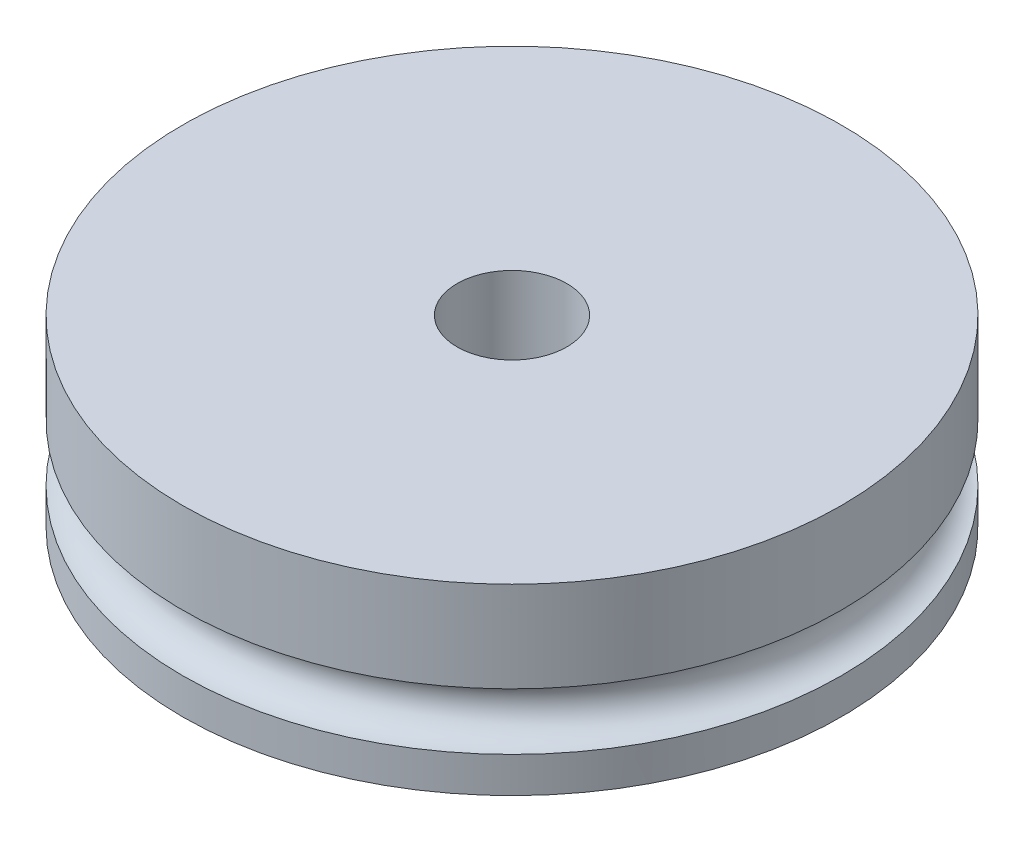
SolidWorks part; units mm, degrees
ref_plane "Front Plane" through (0, 0, 0) normal (0, 0, 1) x (1, 0, 0)
ref_plane "Top Plane" through (0, 0, 0) normal (0, 1, 0) x (1, 0, 0)
ref_plane "Right Plane" through (0, 0, 0) normal (1, 0, 0) x (0, 0, -1)
sketch "Sketch1" plane through (0, 0, 0) normal (0, 1, 0) x (1, 0, 0)
  circle A0 centre (0, 0) radius 18
  dimension "D1" = 36
extrude "Boss-Extrude1" add sketch "Sketch1" along normal blind 10
sketch "Sketch2" plane through (0, 0, 0) normal (0, 0, 1) x (1, 0, 0)
  line L0 (0, 0) -> (0, 10) construction
  line L1 (-18, 0) -> (18, 0) construction
  line L2 (18, 10) -> (-18, 10) construction
  line L3 (0, 3.5) -> (18, 3.5) construction
  line L4 (18, 0) -> (18, 10) construction
  circle A0 centre (18, 3.5) radius 1.55
  dimension "D2" = 3.1
  dimension "D1" = 3.5
revolve "Cut-Revolve1" cut sketch "Sketch2" angle 360 about L0
sketch "Sketch4" plane through (0, 10, 0) normal (0, 1, 0) x (1, 0, 0)
  line L0 (0.6312, 2.3155) -> (-0.789, -2.8944) construction
  line L2 (-2.8944, 0.789) -> (2.8944, -0.789) construction
  circle A0 centre (0, 0) radius 3
  point P6 (0, 0)
  dimension "D1" = 6
extrude "Cut-Extrude1" cut sketch "Sketch4" against normal blind 8
